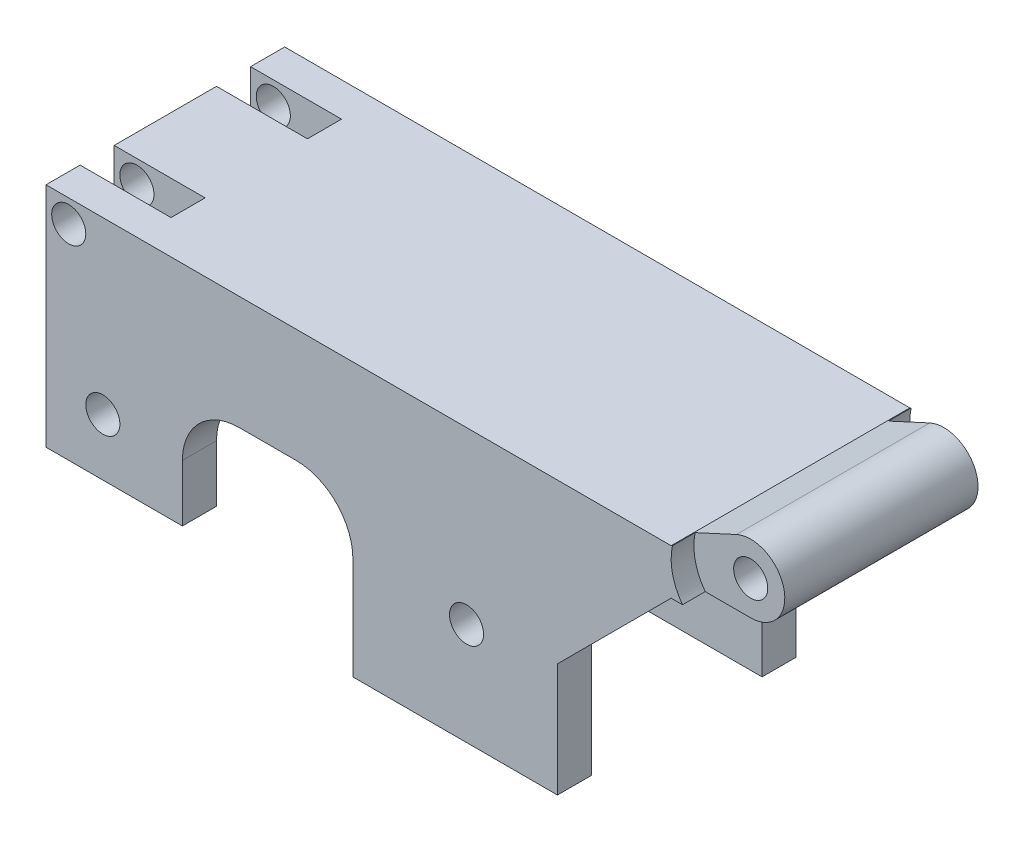
SolidWorks part; units mm, degrees
ref_plane "前视基准面" through (0, 0, 0) normal (0, 0, 1) x (1, 0, 0)
ref_plane "上视基准面" through (0, 0, 0) normal (0, 1, 0) x (1, 0, 0)
ref_plane "右视基准面" through (0, 0, 0) normal (1, 0, 0) x (0, 0, -1)
sketch "草图1" plane through (0, 0, 0) normal (0, 0, 1) x (1, 0, 0)
  line L0 (0, -3) -> (-60, -3)
  line L1 (-60, -3) -> (-60, 1)
  line L2 (-1.255, 2.7249) -> (-5, 1)
  line L3 (-5, 1) -> (-60, 1)
  circle A0 centre (0, 0) radius 1.5
  circle A1 centre (0, 0) radius 3
  dimension "D1" = 3
  dimension "D2" = 6
  dimension "D3" = 4
  dimension "D4" = 55
  dimension "D5" = 60
extrude "凸台-拉伸1" add sketch "草图1" along normal blind 25 contours A1 L2 L3 L1 L0 | A1 A0
sketch "草图2" plane through (0, 0, 25) normal (0, 0, 1) x (1, 0, 0)
  line L0 (-60, -3) -> (-60, -19)
  line L1 (-60, -3) -> (-60, 1) construction
  line L2 (-60, -19) -> (-48, -19)
  line L3 (-48, -19) -> (-48, -14)
  line L4 (-43, -9) -> (-38, -9)
  line L5 (-33, -14) -> (-33, -23)
  line L6 (-33, -23) -> (-15, -23)
  line L7 (-15, -23) -> (-15, -13)
  line L8 (-15, -13) -> (-5, -3)
  line L9 (-60, -3) -> (-5, -3)
  line L10 (0, -3) -> (-60, -3) construction
  arc A0 (-38, -9) -> (-33, -14) centre (-38, -14) cw
  arc A1 (-48, -14) -> (-43, -9) centre (-43, -14) cw
  point P13 (-33, -9)
  point P16 (-48, -9)
  dimension "D4" = 5
  dimension "D1" = 12
  dimension "D2" = 18
  dimension "D3" = 15
  dimension "D5" = 16
  dimension "D6" = 20
  dimension "D7" = 6
  dimension "D8" = 10
extrude "凸台-拉伸2" add sketch "草图2" against normal blind 5
sketch "草图3" plane through (0, 0, 25) normal (0, 0, 1) x (1, 0, 0)
  line L0 (-60, -19) -> (-48, -19) construction
  line L1 (-60, -19) -> (-60, 1) construction
  line L2 (-15, -23) -> (-15, -13) construction
  line L3 (-33, -23) -> (-15, -23) construction
  circle A0 centre (-55, -14) radius 1.5
  circle A1 centre (-23, -14) radius 1.5
  dimension "D1" = 3
  dimension "D2" = 3
  dimension "D3" = 5
  dimension "D4" = 5
  dimension "D5" = 8
  dimension "D6" = 9
extrude "切除-拉伸1" cut sketch "草图3" against normal through all
sketch "草图4" plane through (0, 0, 25) normal (0, 0, 1) x (1, 0, 0)
  circle A0 centre (0, 0) radius 5
  dimension "D1" = 10
extrude "切除-拉伸2" cut sketch "草图4" against normal blind 4
sketch "草图5" plane through (0, 0, 0) normal (0, 0, -1) x (-1, 0, 0)
  line L9 (60, -3) -> (5, -3)
  line L10 (5, -3) -> (15, -13)
  line L11 (15, -13) -> (15, -23)
  line L12 (15, -23) -> (33, -23)
  line L13 (33, -23) -> (33, -14)
  line L14 (38, -9) -> (43, -9)
  line L15 (48, -14) -> (48, -19)
  line L16 (48, -19) -> (60, -19)
  line L17 (60, -19) -> (60, -3)
  line L18 (60, -3) -> (5, -3)
  line L19 (5, -3) -> (15, -13)
  line L20 (15, -13) -> (15, -23)
  line L21 (15, -23) -> (33, -23)
  line L22 (33, -23) -> (33, -14)
  line L23 (38, -9) -> (43, -9)
  line L24 (48, -14) -> (48, -19)
  line L25 (48, -19) -> (60, -19)
  line L26 (60, -19) -> (60, -3)
  circle A0 centre (23, -14) radius 1.5
  circle A1 centre (55, -14) radius 1.5
  arc A2 (38, -9) -> (33, -14) centre (38, -14) ccw
  arc A3 (48, -14) -> (43, -9) centre (43, -14) ccw
  arc A4 (38, -9) -> (33, -14) centre (38, -14) ccw
  arc A5 (48, -14) -> (43, -9) centre (43, -14) ccw
  dimension "D1" = 0
extrude "凸台-拉伸3" add sketch "草图5" against normal blind 5
sketch "草图6" plane through (0, 0, 0) normal (0, 0, -1) x (-1, 0, 0)
  circle A0 centre (0, 0) radius 5
  dimension "D1" = 10
extrude "切除-拉伸3" cut sketch "草图6" against normal blind 4
sketch "草图7" plane through (0, 1, 0) normal (0, 1, 0) x (1, 0, 0)
  line L0 (-60, -25) -> (-60, 0) construction
  line L1 (-52, -5) -> (-60, -5)
  line L2 (-52, -5) -> (-52, -8)
  line L3 (-52, -8) -> (-60, -8)
  line L4 (-60, -5) -> (-60, -8)
  line L5 (-52, -17) -> (-60, -17)
  line L6 (-52, -17) -> (-52, -20)
  line L7 (-52, -20) -> (-60, -20)
  line L8 (-60, -17) -> (-60, -20)
  line L9 (-14.3, 0) -> (14.3, 0) construction
  dimension "D1" = 3
  dimension "D2" = 3
  dimension "D3" = 9
  dimension "D4" = 8
  dimension "D5" = 8
  dimension "D6" = 5
extrude "切除-拉伸4" cut sketch "草图7" against normal through all
sketch "草图8" plane through (0, 0, 0) normal (0, 0, -1) x (-1, 0, 0)
  line L0 (60, -19) -> (60, 1) construction
  line L1 (5, 1) -> (60, 1) construction
  circle A0 centre (58, -1) radius 1.5
  dimension "D1" = 3
  dimension "D2" = 2
  dimension "D3" = 2
extrude "切除-拉伸5" cut sketch "草图8" against normal through all
sketch "草图9" plane through (0, 0, 0) normal (0, 0, -1) x (-1, 0, 0)
  line L1 (2.196, -32.9407) -> (64.2413, -32.9407)
  line L2 (2.196, -32.9407) -> (2.196, 14.2458)
  line L3 (2.196, 14.2458) -> (64.2413, 14.2458)
  line L4 (64.2413, -32.9407) -> (64.2413, 14.2458)
extrude "切除-拉伸6" cut sketch "草图9" against normal blind 2
sketch "草图10" plane through (0, 0, 25) normal (0, 0, 1) x (1, 0, 0)
  circle A0 centre (-29.0133, -5.8649) radius 43.3213
extrude "切除-拉伸7" cut sketch "草图10" against normal blind 2
